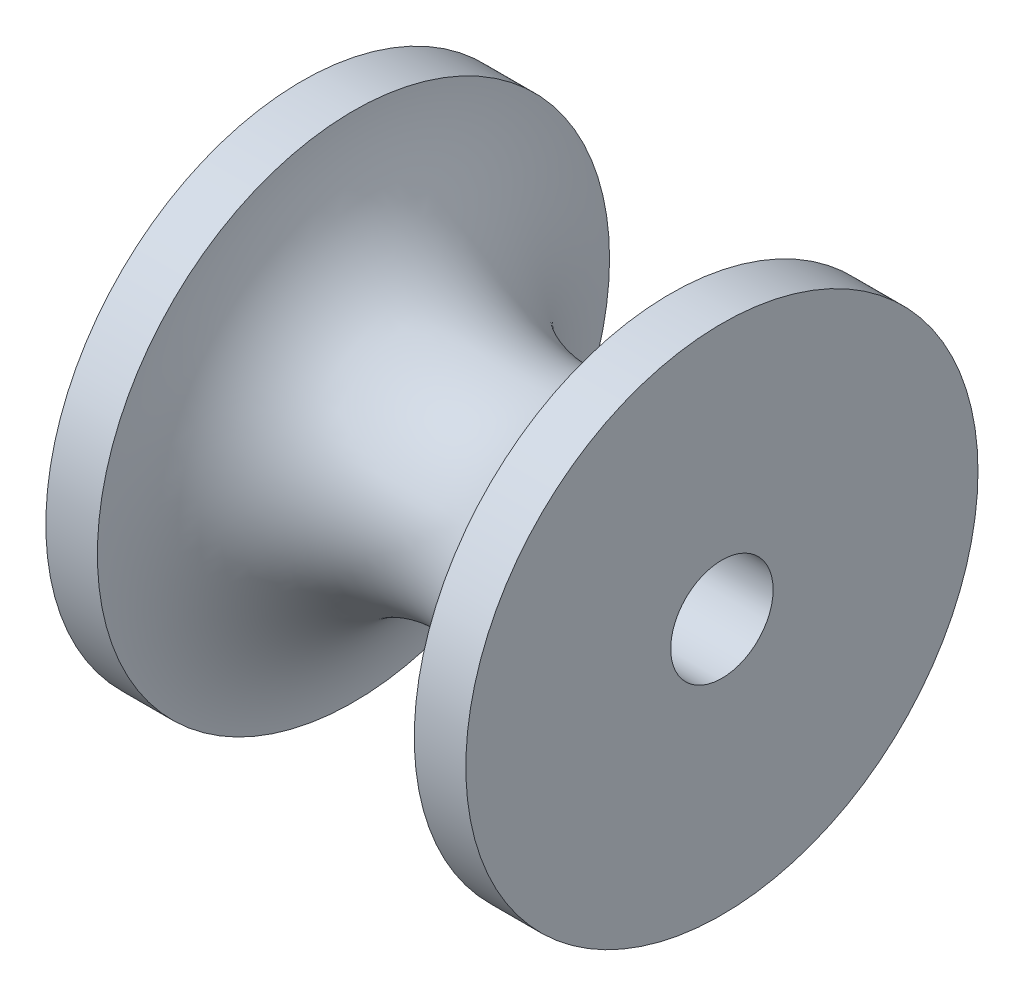
SolidWorks part; units mm, degrees
ref_plane "Front Plane" through (0, 0, 0) normal (0, 0, 1) x (1, 0, 0)
ref_plane "Top Plane" through (0, 0, 0) normal (0, 1, 0) x (1, 0, 0)
ref_plane "Right Plane" through (0, 0, 0) normal (1, 0, 0) x (0, 0, -1)
sketch "Sketch1" plane through (0, 0, 0) normal (0, 0, 1) x (1, 0, 0)
  line L0 (0, 14.6374) -> (0, 8) construction
  line L1 (4.1, 1) -> (-4.1, 1)
  line L2 (4.1, 1) -> (4.1, 5)
  line L3 (4.1, 5) -> (3.0935, 5)
  line L4 (-4.1, 1) -> (-4.1, 5)
  line L5 (4.1, 1) -> (-4.1, 5) construction
  line L6 (4.1, 5) -> (-4.1, 1) construction
  line L7 (-3.0935, 5) -> (-4.1, 5)
  line L8 (0, 3) -> (0, -2.045) construction
  line L9 (11.8573, 0) -> (-10.8747, 0) construction
  arc A0 (-3.0935, 5) -> (3.0935, 5) centre (0, 5.2) ccw
  point P0 (0, 3)
  dimension "D4" = 3.1
  dimension "D1" = 8.2
  dimension "D2" = 4
  dimension "D3" = 1
  dimension "D5" = 0.2
revolve "Revolve1" add sketch "Sketch1" angle 360 about L9
